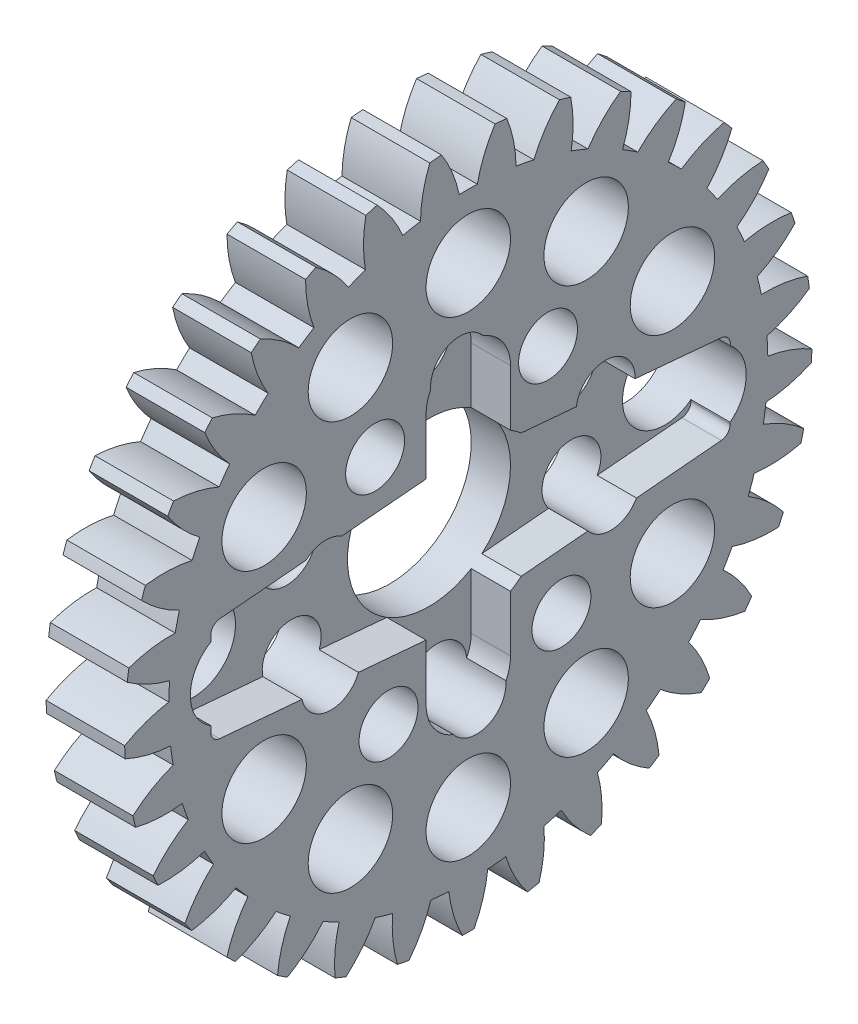
SolidWorks part; units mm, degrees
ref_plane "Plane1" through (0, 0, 0) normal (0, 0, 1) x (1, 0, 0)
ref_plane "Plane2" through (0, 0, 0) normal (0, 1, 0) x (1, 0, 0)
ref_plane "Plane3" through (0, 0, 0) normal (1, 0, 0) x (0, 0, -1)
sketch "HoldingSke" plane through (0, 0, 0) normal (0, 1, 0) x (1, 0, 0)
  line L0 (0, 0) -> (0.8387, -0.5446)
  line L1 (-15, 0) -> (100, 0) construction
  line L2 (0, 0) -> (-2.1039, 2.3779)
  line L3 (0, 0) -> (-11.863, 4.5341)
  line L4 (0, 0) -> (7.2428, 4.7035)
  line L5 (0, 0) -> (-46.8476, -17.4728)
  line L6 (0, 0) -> (-3.3159, -2.2372)
  line L7 (-2.1039, 2.3779) -> (8.6586, 51.2059)
  line L8 (-76.2, 54.61) -> (-75.7, 54.61)
  line L9 (-71.009, 38.7566) -> (-53.1078, 45.2721)
  line L10 (-76.2, 71.12) -> (104.1128, 71.12)
  line L11 (0, 0) -> (-4, 0)
  line L12 (-76.2, 101.6) -> (-76.162, 101.6)
  line L13 (24.9733, 27.94) -> (52.9518, 28.4284)
  line L14 (24.9733, 27.94) -> (24.9743, 27.94)
  line L15 (24.9733, 27.94) -> (100.4006, 29.5858)
  line L16 (-63.627, -1) -> (-12.827, -1)
  circle A0 centre (0, 0) radius 1.5
  circle A1 centre (0, 0) radius 15.249
  circle A2 centre (0, 0) radius 37.5
  circle A3 centre (0, 0) radius 1.5
  dimension "MHD" = 30.498
  dimension "Hub_dia" = 75
  dimension "Bore" = 3
  dimension "MBD" = 3
  dimension "Num_teeth" = 33
  dimension "Pitch_radius" = 180.3128
  dimension "Pitch" = 1
  dimension "Width" = 4
  dimension "Overall_len" = 50
  dimension "Show_teeth" = 33
  dimension "Thickness" = 4
  dimension "OAL" = 50.0001
  dimension "T_dim" = 0.5
  dimension "Ap" = 20
  dimension "H" = 19.05
  dimension "Backlash" = 0.038
  dimension "Addendum_fac" = 1
  dimension "Dedendum_fac" = 1.25
  dimension "Clearance_fac" = 0.25
  dimension "Dedendum_add" = 0.001
  dimension "Module" = 1
sketch "BasProSke" plane through (0, 0, 0) normal (0, 1, 0) x (1, 0, 0)
  line L0 (-10, 0) -> (60, 0) construction
  line L1 (0, 0) -> (0, 17.5)
  line L2 (0, 0) -> (4, 0)
  line L3 (4, 0) -> (4, 17.5)
  line L4 (4, 17.5) -> (0, 17.5)
  dimension "Diameter" = 35
  dimension "Thickness" = 4
revolve "Base-Revolve" add sketch "BasProSke" angle 360 about L0
sketch "TooCutSke" plane through (0, 0, 0) normal (1, 0, 0) x (0, 0, -1)
  line L1 (0, 0) -> (0, 107) construction
  line L2 (0, 0) -> (-0.8516, 16.478) construction
  line L3 (0, 0) -> (-3.1339, 32.8194) construction
  line L4 (-0.8516, 16.478) -> (-1.5669, 16.4097) construction
  arc A0 (0.46, 15.2421) -> (-0.46, 15.2421) centre (0, 0) ccw
  arc A1 (1.3819, 17.4708) -> (-1.3819, 17.4708) centre (0, 0) ccw
  circle A2 centre (0, 0) radius 16.5 construction
  circle A3 centre (0, 0) radius 15.5049 construction
  arc A4 (-0.46, 15.2421) -> (-1.3819, 17.4708) centre (-6.9172, 13.8764) ccw
  arc A5 (1.3819, 17.4708) -> (0.46, 15.2421) centre (6.9172, 13.8764) ccw
  dimension "Root_dia" = 30.498
  dimension "Overcut_dia" = 35.0508
  dimension "Pitch_dia" = 33
  dimension "Base_dia" = 31.0099
  dimension "Flank_rad" = 6.6
  dimension "Half_ang" = 5.455
  dimension "Half_CT" = 0.7186
extrude "ToothCut" cut sketch "TooCutSke" along normal through all
fillet "Breaks" [suppressed] radius 0.02
fillet "RootFillets" [suppressed] radius 0.251
pattern_circular "TeethCuts" count 33 every 10.909 about axis through (-10, 0, 0) along (1, 0, 0) of "ToothCut", "RootFillets", "Breaks"
sketch "HubNeaOneSke" plane through (0, 0, 0) normal (-1, 0, 0) x (0, 0, 1)
  circle A0 centre (0, 0) radius 15.249
  dimension "Diameter" = 30.498
extrude "HubNearOne" [suppressed] add sketch "HubNeaOneSke" along normal blind 46.0001
sketch "HubNeaBotSke" plane through (0, 0, 0) normal (-1, 0, 0) x (0, 0, 1)
  circle A0 centre (0, 0) radius 15.249
  dimension "Diameter" = 30.498
extrude "HubNearBoth" [suppressed] add sketch "HubNeaBotSke" along normal blind 23
ref_plane "FarPln" through (4, 0, 0) normal (1, 0, 0) x (0, 0, -1)
sketch "HubFarSke" plane through (4, 0, 0) normal (1, 0, 0) x (0, 0, -1)
  circle A0 centre (0, 0) radius 15.249
  dimension "Diameter" = 30.498
extrude "HubFar" [suppressed] add sketch "HubFarSke" along normal blind 23
sketch "BorSke" plane through (0, 0, 0) normal (1, 0, 0) x (0, 0, -1)
  circle A0 centre (0, 0) radius 1.5
  dimension "Diameter" = 3
extrude "Bore" cut sketch "BorSke" along normal mid plane 100.0001
sketch "KeySke" plane through (0, 0, 0) normal (1, 0, 0) x (0, 0, -1)
  line L0 (-0.6, 0) -> (-0.6, 2)
  line L1 (-0.6, 2) -> (0.6, 2)
  line L2 (0.6, 2) -> (0.6, 0)
  line L3 (0, 0) -> (0, 34) construction
  line L4 (-0.6, 0) -> (0.6, 0)
  dimension "Offset" = 2
  dimension "Width" = 1.2
extrude "Keyway" [suppressed] cut sketch "KeySke" along normal mid plane 100.0001
pattern_circular "Keyway2" [suppressed] count 2 every 90 about axis through (-10, 0, 0) along (1, 0, 0)
sketch "flap2-" plane through (4, 0, 0) normal (1, 0, 0) x (0, 0, -1)
  line L0 (0, 6.4) -> (0, -6.4) construction
  line L1 (2.15, 6.4) -> (2.15, -6.4)
  line L2 (-2.15, 6.4) -> (-2.15, -6.4)
  line L3 (0, 0) -> (20.8674, 0) construction
  arc A0 (2.15, 6.4) -> (-2.15, 6.4) centre (0, 6.4) ccw
  arc A1 (-2.15, -6.4) -> (2.15, -6.4) centre (0, -6.4) ccw
  point P3 (0, 0)
  dimension "D1" = 6.4
  dimension "D2" = 12.8
  dimension "D3" = 4.3
extrude "flap" cut sketch "flap2-" against normal blind 2
sketch "flap2" plane through (4, 0, 0) normal (1, 0, 0) x (0, 0, -1)
  line L0 (-12.7118, 3.6) -> (12.4854, 3.6) construction
  line L1 (-12.7118, -3.6) -> (12.7675, -3.6) construction
  line L2 (-12.7118, 0) -> (12.7675, 0) construction
  line L3 (-2.15, 3.5496) -> (-13.1093, 2.6043)
  line L4 (-2.15, 6.4) -> (-2.15, -6.4) construction
  line L5 (-2.15, -3.5496) -> (-13.1093, -2.6043)
  line L7 (-13.1093, 2.6043) -> (-13.1093, -2.6043)
  line L8 (-2.15, 3.5496) -> (-2.15, -3.5496)
  circle A0 centre (0, 0) radius 4.15 construction
  dimension "D1" = 3.6
  dimension "8.3" = 8.3
  dimension "D2" = 3.6
  dimension "D3" = 4.93
  dimension "D4" = 4.93
  dimension "D5" = 11
  dimension "D6" = 11
extrude "flap-2" cut sketch "flap2" against normal blind 2
sketch "flap3" plane through (4, 0, 0) normal (1, 0, 0) x (0, 0, -1)
  line L0 (0, 0) -> (15.1307, 0) construction
  line L1 (0.4928, 3.16) -> (13.2987, 3.16) construction
  line L2 (0.4928, -3.16) -> (13.2987, -3.16) construction
  line L3 (2.6901, -3.16) -> (13.332, -2.2233)
  line L4 (2.6901, 3.16) -> (13.3407, 2.2226)
  line L5 (13.3407, 2.2226) -> (13.332, -2.2233)
  line L6 (2.6901, 3.16) -> (2.6901, -3.16)
  circle A0 centre (0, 0) radius 4.15 construction
  dimension "D1" = 8.3
  dimension "D2" = 3.16
  dimension "D3" = 3.16
  dimension "D4" = 6.32
  dimension "D5" = 5.03
  dimension "D6" = 5.03
extrude "flap-3" cut sketch "flap3" against normal blind 2
sketch "bore-8.3" plane through (4, 0, 0) normal (1, 0, 0) x (0, 0, -1)
  circle A0 centre (0, 0) radius 4.15
  dimension "D1" = 8.3
extrude "bore8.3" cut sketch "bore-8.3" against normal through all
fillet "Verrundung1" radius 0.5 4 edges at (3, 2.6043, 13.1093) (3, -2.6043, 13.1093) (3, 2.2226, -13.3407) (3, -2.2233, -13.332)
sketch "Skizze1" plane through (4, 0, 0) normal (1, 0, 0) x (0, 0, -1)
  circle A0 centre (0, 0) radius 12 construction
  circle A1 centre (-12, 0) radius 2.15
  dimension "D1" = 24
  dimension "D2" = 4.3
extrude "Schnitt-Linear austragen1" cut sketch "Skizze1" against normal through all
pattern_circular "Kreismuster1" count 12 over 360 about axis through (0, 0, 0) along (1, 0, 0) of "Schnitt-Linear austragen1"
sketch "Skizze2" plane through (4, 0, 0) normal (1, 0, 0) x (0, 0, -1)
  circle A0 centre (0, 0) radius 7.5 construction
  circle A1 centre (-4.7424, 5.8103) radius 1.5
  dimension "D1" = 15
  dimension "D2" = 3
extrude "Schnitt-Linear austragen2" cut sketch "Skizze2" against normal through all
pattern_circular "Kreismuster2" count 10 over 360 about axis through (0, 0, 0) along (1, 0, 0) of "Schnitt-Linear austragen2"
equation "' \"Module@HoldingSke\" = 6.35"
equation "' \"Num_teeth@HoldingSke\" = 12"
equation "' \"Ap@HoldingSke\" =  20"
equation "' \"Width@HoldingSke\" = 0.5 * 25.4"
equation "' \"Hub_dia@HoldingSke\"= 1 * 25.4"
equation "' \"Overall_len@HoldingSke\" = 1.0 * 25.4"
equation "' \"Bore@HoldingSke\" = 0.75 * 25.4"
equation "' \"T_dim@HoldingSke\" = 0.1 * 25.4"
equation "' \"Width@KeySke\" = 0.25 * 25.4"
equation "' \"Show_teeth@HoldingSke\" = 13"
equation "' \"Backlash@HoldingSke\" = 0.009 * 25.4"
equation "' \"Addendum_fac@HoldingSke\" = 1.0"
equation "' \"Dedendum_fac@HoldingSke\" = 1.25"
equation "' \"Dedendum_add@HoldingSke\" = 0.00005 * 25.4"
equation "' \"Clearance_fac@HoldingSke\" = 0.25"
equation "\"Pitch@HoldingSke\" = 1 / \"Module@HoldingSke\""
equation "\"Overcut_dia@TooCutSke\" = (\"Num_teeth@HoldingSke\" + 2 * \"Addendum_fac@HoldingSke\") / \"Pitch@HoldingSke\" + 0.002 * 25.4"
equation "\"Pitch_dia@TooCutSke\" = \"Num_teeth@HoldingSke\" / \"Pitch@HoldingSke\""
equation "\"Base_dia@TooCutSke\" = \"Num_teeth@HoldingSke\" / \"Pitch@HoldingSke\" * cos((\"Ap@HoldingSke\"  * 3.14159265 / 180))"
equation "\"Root_dia@TooCutSke\" = (\"Num_teeth@HoldingSke\" + 2) / \"Pitch@HoldingSke\" - 2 * (\"Addendum_fac@HoldingSke\" + \"Dedendum_fac@HoldingSke\") / \"Pitch@HoldingSke\" - \"Dedendum_add@HoldingSke\" * 2"
equation "\"Half_ang@TooCutSke\" = 180 / \"Num_teeth@HoldingSke\""
equation "\"Half_CT@TooCutSke\" = \"Num_teeth@HoldingSke\" / \"Pitch@HoldingSke\" * sin((3.14159265 / 2 / \"Num_teeth@HoldingSke\")) / 2 - 7 * \"Backlash@HoldingSke\" / 4"
equation "\"Flank_rad@TooCutSke\" = \"Num_teeth@HoldingSke\" / \"Pitch@HoldingSke\" / 5"
equation "\"Radius@RootFillets\" = \"Clearance_fac@HoldingSke\" / \"Pitch@HoldingSke\" + \"Dedendum_add@HoldingSke\""
equation "\"Break_rad@Breaks\" = 0.02 / \"Pitch@HoldingSke\""
equation "\"Thickness@HoldingSke\" = \"Width@HoldingSke\""
equation "\"OAL@HoldingSke\" = \"Thickness@HoldingSke\""
equation "\"MHD@HoldingSke\" = (\"Num_teeth@HoldingSke\" + 2) / \"Pitch@HoldingSke\" - 2 * (\"Addendum_fac@HoldingSke\" + \"Dedendum_fac@HoldingSke\")  / \"Pitch@HoldingSke\" - \"Dedendum_add@HoldingSke\" * 2"
equation "\"MBD@HoldingSke\" = (\"Num_teeth@HoldingSke\" + 2) / \"Pitch@HoldingSke\" - 2 * (\"Addendum_fac@HoldingSke\" + \"Dedendum_fac@HoldingSke\")  / \"Pitch@HoldingSke\" - \"Dedendum_add@HoldingSke\" * 2 - 0.002 * 25.4"
equation "\"MHD@HoldingSke\" = ((sgn( \"MHD@HoldingSke\" - \"Hub_dia@HoldingSke\" )-1)*( \"MHD@HoldingSke\" - \"Hub_dia@HoldingSke\" ))/-2+ \"Hub_dia@HoldingSke\""
equation "\"MBD@HoldingSke\" = ((sgn( \"MBD@HoldingSke\" - \"Bore@HoldingSke\" )-1)*( \"MBD@HoldingSke\" - \"Bore@HoldingSke\" ))/-2+ \"Bore@HoldingSke\""
equation "\"OAL@HoldingSke\" = ((sgn( \"OAL@HoldingSke\" - \"Overall_len@HoldingSke\" )+1)*( \"OAL@HoldingSke\" - \"Overall_len@HoldingSke\" ))/2 + \"Overall_len@HoldingSke\" + 0.000002 * 25.4"
equation "\"Num_teeth@TeethCuts\" = int( \"Show_teeth@HoldingSke\" ) + 1"
equation "\"Num_teeth@TeethCuts\" = ((sgn( \"Num_teeth@TeethCuts\" - \"Num_teeth@HoldingSke\" )-1)*( \"Num_teeth@TeethCuts\" - \"Num_teeth@HoldingSke\" ))/-2+ \"Num_teeth@HoldingSke\""
equation "\"Num_teeth@TeethCuts\" = ((sgn( \"Num_teeth@TeethCuts\" - 2.0)+1)*( \"Num_teeth@TeethCuts\" - 2.0))/2 +2.0"
equation "\"Angle@TeethCuts\" = 360.0 / \"Num_teeth@HoldingSke\""
equation "\"Diameter@BasProSke\" = (\"Num_teeth@HoldingSke\" + 2 * \"Addendum_fac@HoldingSke\") / \"Pitch@HoldingSke\""
equation "\"Thickness@BasProSke\"  = \"Thickness@HoldingSke\""
equation "' \"Fillet_rad@BasProSke\" =  \"Thickness@HoldingSke\" * 0.05"
equation "\"MHD@HoldingSke\" = ((sgn( \"MHD@HoldingSke\" - \"Root_dia@TooCutSke\" )-1)*( \"MHD@HoldingSke\" - \"Root_dia@TooCutSke\" ))/-2+ \"Root_dia@TooCutSke\""
equation "\"Diameter@HubNeaOneSke\" = \"MHD@HoldingSke\""
equation "\"Length@HubNearOne\" = \"OAL@HoldingSke\" - \"Thickness@BasProSke\""
equation "\"Diameter@HubNeaBotSke\" = \"MHD@HoldingSke\""
equation "\"Length@HubNearBoth\" = ( \"OAL@HoldingSke\" - \"Thickness@BasProSke\" ) / 2.0"
equation "\"Thickness@FarPln\" = \"Thickness@BasProSke\""
equation "\"Diameter@HubFarSke\" = \"MHD@HoldingSke\""
equation "\"Length@HubFar\" = ( \"OAL@HoldingSke\" - \"Thickness@BasProSke\" ) / 2.0"
equation "\"Diameter@BorSke\" = \"MBD@HoldingSke\""
equation "\"D1@Bore\" = \"OAL@HoldingSke\" * 2.0"
equation "\"D1@Keyway\" = \"OAL@HoldingSke\" * 2.0"
equation "\"Offset@KeySke\" = \"T_dim@HoldingSke\" + \"MBD@HoldingSke\" / 2.0"
